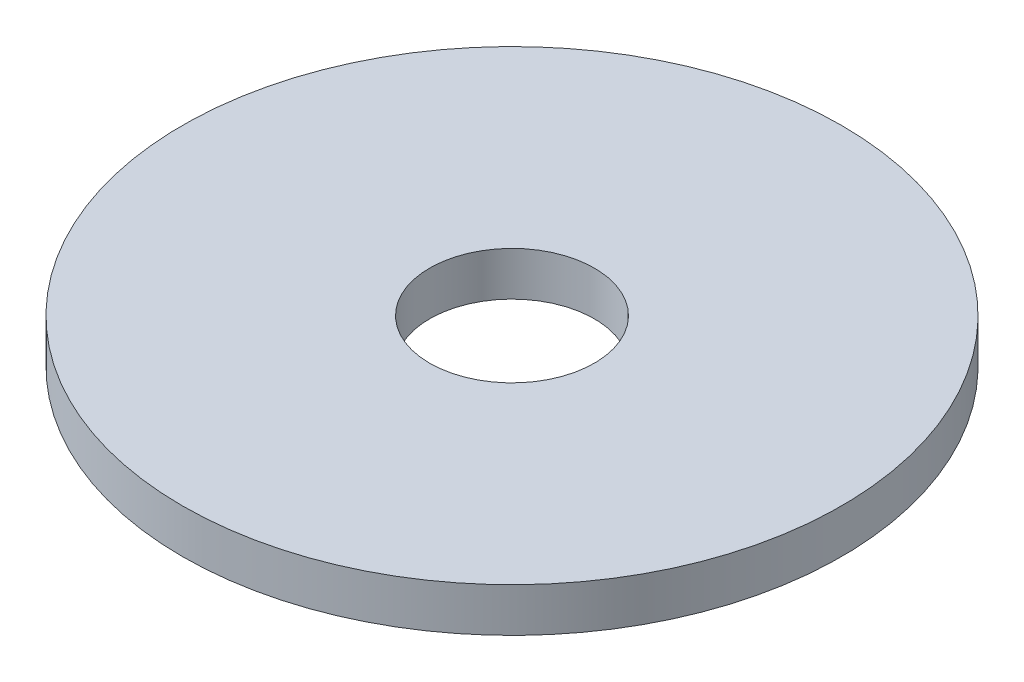
SolidWorks part; units mm, degrees
ref_plane "Front Plane" through (0, 0, 0) normal (0, 0, 1) x (1, 0, 0)
ref_plane "Top Plane" through (0, 0, 0) normal (0, 1, 0) x (1, 0, 0)
ref_plane "Right Plane" through (0, 0, 0) normal (1, 0, 0) x (0, 0, -1)
sketch "Sketch1" plane through (0, 0, 0) normal (0, 0, 1) x (1, 0, 0)
  line L0 (0, 2.3401) -> (0, -2.1072) construction
  line L1 (1.875, 1) -> (1.875, 0)
  line L2 (1.875, 0) -> (7.5, 0)
  line L3 (7.5, 0) -> (7.5, 1)
  line L4 (7.5, 1) -> (1.875, 1)
  dimension "D1" = 1
  dimension "D2" = 7.5
  dimension "D3" = 1.875
revolve "Revolve1" add sketch "Sketch1" angle 360 about L0
